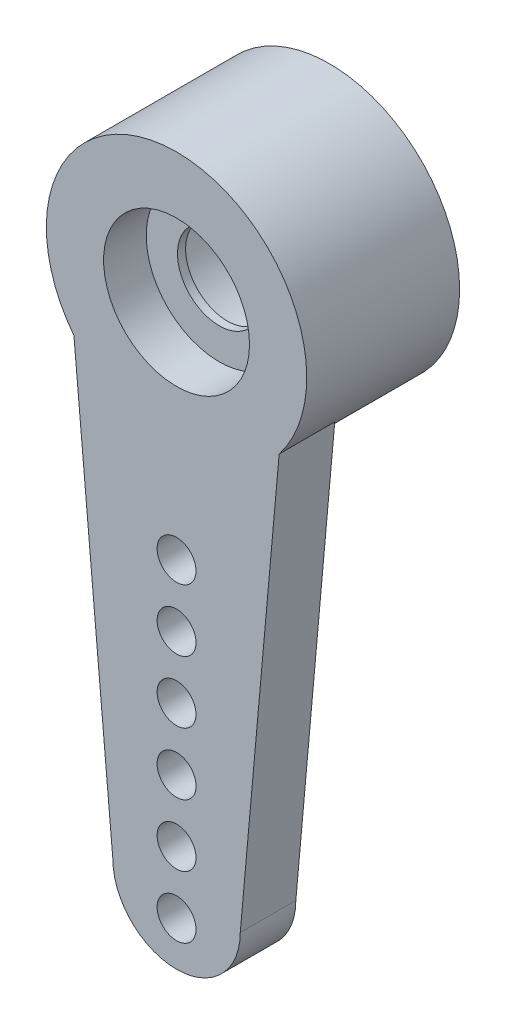
SolidWorks part; units mm, degrees
material "Nylon 6/10"
ref_plane "Front Plane" through (0, 0, 0) normal (0, 0, 1) x (1, 0, 0)
ref_plane "Top Plane" through (0, 0, 0) normal (0, 1, 0) x (1, 0, 0)
ref_plane "Right Plane" through (0, 0, 0) normal (1, 0, 0) x (0, 0, -1)
ref_plane "Plane1" through (0, 0, -7.033) normal (0, 0, 1) x (1, 0, 0)
sketch "Sketch1" plane through (0, 0, -7.033) normal (0, 0, 1) x (1, 0, 0)
  circle A0 centre (-5.5, 0) radius 3.5687
  circle A1 centre (-5.5, 0) radius 2
  dimension "D1" = 7.1374
extrude "Boss-Extrude1" add sketch "Sketch1" along normal blind 4.191
sketch "Sketch5" plane through (0, 0, -4.233) normal (0, 0, 1) x (1, 0, 0)
  circle A0 centre (-5.5, 0) radius 1.143
  circle A1 centre (-5.5, 0) radius 2 construction
  circle A2 centre (-5.5, 0) radius 2
  dimension "D1" = 2.286
extrude "Boss-Extrude2" add sketch "Sketch5" along normal offset from surface (0.2226 mm away) 1.1684 up to face at (-1.9313, 0, -2.842)
sketch "Sketch6" plane through (0, 0, -2.842) normal (0, 0, 1) x (1, 0, 0)
  line L0 (-3.7537, -14.0907) -> (-2.6869, -2.196)
  line L1 (-7.2462, -14.0907) -> (-8.313, -2.196)
  line L2 (-5.5, 0) -> (-5.5, -14.0907) construction
  line L3 (-5.5, -14.6241) -> (-5.5, -12.9223) construction
  arc A0 (-7.2462, -14.0907) -> (-3.7537, -14.0907) centre (-5.5, -14.0907) ccw
  circle A1 centre (-5.5, 0) radius 3.5687 construction
  circle A2 centre (-5.5, 0) radius 3.5687 construction
  circle A3 centre (-5.5, -12.9223) radius 0.5334
  circle A4 centre (-5.5, -14.6241) radius 0.5334
  circle A5 centre (-5.5, -11.2205) radius 0.5334
  circle A6 centre (-5.5, -9.5186) radius 0.5334
  circle A7 centre (-5.5, -7.8169) radius 0.5334
  circle A8 centre (-5.5, -6.1151) radius 0.5334
  arc A9 (-2.6869, -2.196) -> (-8.313, -2.196) centre (-5.5, 0) cw
  dimension "D1" = 3.4925
  dimension "D2" = 15.8369
  dimension "D4" = 1.0668
  dimension "D3" = 5.6261
  dimension "D6" = 1.7018
  dimension "D5" = 6
extrude "Boss-Extrude3" add sketch "Sketch6" against normal blind 1.524
